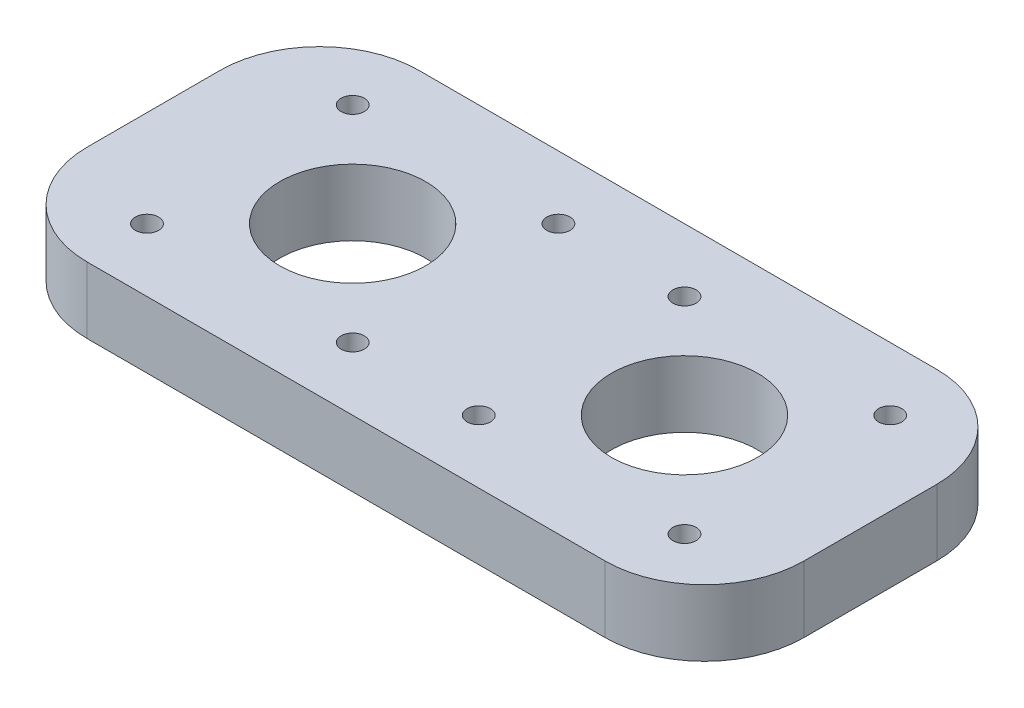
SolidWorks part; units mm, degrees
ref_plane "Front Plane" through (0, 0, 0) normal (0, 0, 1) x (1, 0, 0)
ref_plane "Top Plane" through (0, 0, 0) normal (0, 1, 0) x (1, 0, 0)
ref_plane "Right Plane" through (0, 0, 0) normal (1, 0, 0) x (0, 0, -1)
sketch "Sketch1" plane through (0, 0, 0) normal (0, 1, 0) x (1, 0, 0)
  line L0 (-67.5, 0) -> (67.5, 0) construction
  line L1 (-80, -25) -> (28.0168, -25)
  line L2 (-80, -25) -> (-80, 25)
  line L3 (-80, 25) -> (28.0168, 25)
  line L5 (-80, -25) -> (80, 25) construction
  line L6 (-80, 25) -> (80, -25) construction
  line L7 (-15.5, -15.5) -> (15.5, -15.5) construction
  line L8 (-15.5, -15.5) -> (-15.5, 15.5) construction
  line L9 (-15.5, 15.5) -> (15.5, 15.5) construction
  line L10 (15.5, -15.5) -> (15.5, 15.5) construction
  line L11 (-15.5, -15.5) -> (15.5, 15.5) construction
  line L12 (-15.5, 15.5) -> (15.5, -15.5) construction
  line L13 (28.0168, 25) -> (28.0168, -25)
  circle A0 centre (0, 0) radius 11
  circle A1 centre (15.5, 15.5) radius 1.75
  circle A2 centre (-15.5, 15.5) radius 1.75
  circle A3 centre (-15.5, -15.5) radius 1.75
  circle A4 centre (15.5, -15.5) radius 1.75
  circle A8 centre (-65.5, 15.5) radius 1.75
  circle A9 centre (-34.5, 15.5) radius 1.75
  circle A10 centre (-34.5, -15.5) radius 1.75
  circle A11 centre (-65.5, -15.5) radius 1.75
  circle A12 centre (-50, 0) radius 11
  point P0 (0, 0)
  point P21 (0, 0)
  dimension "D3" = 22
  dimension "D5" = 3.5
  dimension "D1" = 160
  dimension "D2" = 50
  dimension "D4" = 31
  dimension "D6" = 2
extrude "Boss-Extrude1" add sketch "Sketch1" along normal blind 10
fillet "Fillet1" radius 15 4 edges at (-80, 5, -25) (-80, 5, 25) (28.0168, 5, -25) (28.0168, 5, 25)
